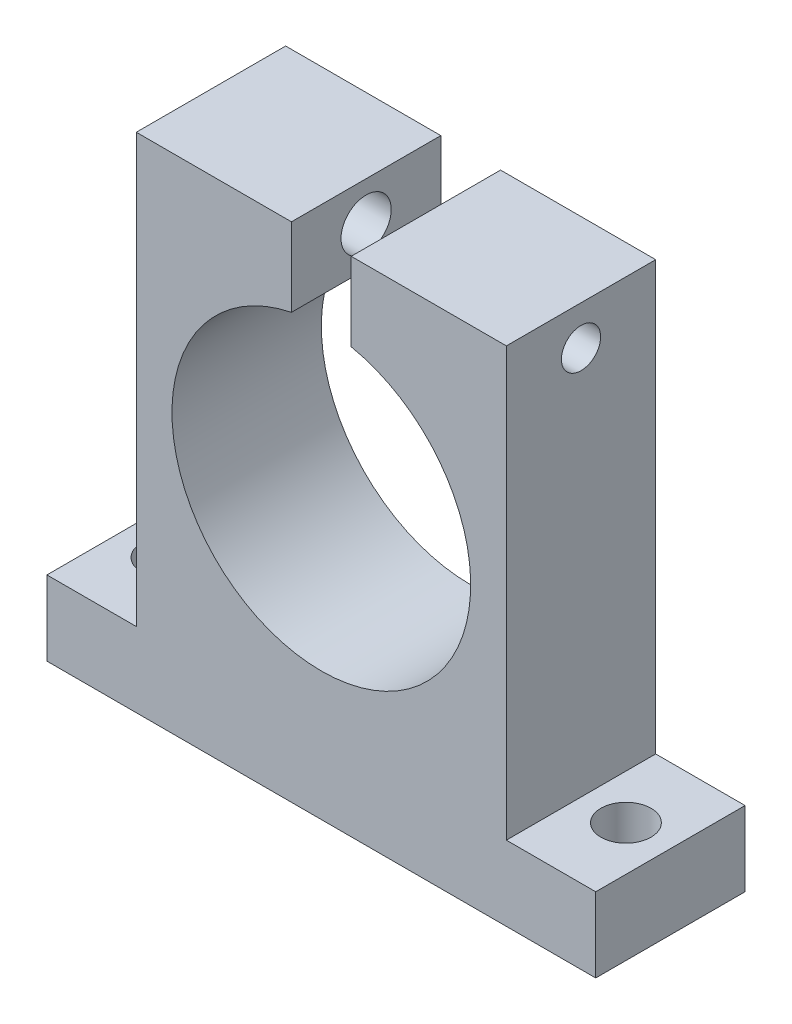
SolidWorks part; units mm, degrees
material "6061-T6 (SS)"
ref_plane "Front" through (0, 0, 0) normal (0, 0, 1) x (1, 0, 0)
ref_plane "Top" through (0, 0, 0) normal (0, 1, 0) x (1, 0, 0)
ref_plane "Right" through (0, 0, 0) normal (1, 0, 0) x (0, 0, -1)
sketch "Sketch7" plane through (0, 0, 0) normal (0, 0, 1) x (1, 0, 0)
  line L0 (-11.8, 14.3326) -> (-1.905, 14.3326)
  line L1 (-17.5, -12.9674) -> (-17.5, -17.7304)
  line L2 (-17.5, -17.7304) -> (17.5, -17.7304)
  line L3 (17.5, -17.7304) -> (17.5, -12.9674)
  line L4 (-1.905, 14.3326) -> (-1.905, 9.3326)
  line L5 (1.905, 14.3326) -> (1.905, 9.3326)
  line L6 (1.905, 14.3326) -> (11.8, 14.3326)
  line L7 (-11.8, 14.3326) -> (-11.8, -12.9674)
  line L8 (-11.8, -12.9674) -> (-17.5, -12.9674)
  line L9 (11.8, 14.3326) -> (11.8, -12.9674)
  line L10 (11.8, -12.9674) -> (17.5, -12.9674)
  line L11 (-1.905, 14.3326) -> (1.905, 14.3326) construction
  line L12 (-11.8, -12.9674) -> (11.8, -12.9674) construction
  arc A0 (-1.905, 9.3326) -> (1.905, 9.3326) centre (0, 0) ccw
  point P1 (-11.8, -12.9674)
  point P3 (9.525, 0)
  point P4 (0, 14.3326)
  point P5 (0, -17.7304)
  point P6 (0, -9.525)
  point P10 (-9.525, 0)
  point P12 (11.8, -12.9674)
  point P15 (-11.8, -12.9674)
  dimension "D1" = 5.7
  dimension "D3" = 27.3
  dimension "D6" = 5
  dimension "D7" = 4.763
  dimension "D2" = 35
  dimension "D5" = 32.063
extrude "Boss-Extrude3" add sketch "Sketch7" along normal blind 9.525
hole_wizard "Tap Drill for M3x0.5 Tap1" positions "Sketch11" profile "Sketch10" hole size "M3x0.5" standard "ANSI Metric" end condition up to next
sketch "Sketch11" plane through (11.8, 0, 0) normal (1, 0, 0) x (0, 0, -1)
  line L0 (-4.7625, 14.3326) -> (-4.7625, -12.9674) construction
  line L1 (-9.525, 14.3326) -> (0, 14.3326) construction
  line L2 (-9.525, -12.9674) -> (0, -12.9674) construction
  point P9 (-4.7625, 11.8326)
  dimension "D1" = 2.5
sketch "Sketch10" plane through (11.8, 11.8326, 4.7625) normal (0, 1, 0) x (0, 0, -1)
  line L0 (0, 0) -> (0, 9.895)
  line L1 (0, 9.895) -> (1.25, 9.895)
  line L2 (1.25, 9.895) -> (1.25, 0)
  line L5 (1.25, 0) -> (0, 0)
  line L11 (0, -6.35) -> (0, 107.95) construction
  dimension "Thru Hole Dia." = 2.5
  dimension "Thru Hole Depth" = 9.895
hole_wizard "M3 Clearance Hole1" positions "Sketch15" profile "Sketch14" hole size "M3" standard "ANSI Metric" end condition through all
sketch "Sketch15" plane through (0, -12.9674, 0) normal (0, 1, 0) x (1, 0, 0)
  line L0 (-11.8, 0) -> (-17.5, 0) construction
  line L1 (-17.5, -9.525) -> (-17.5, 0) construction
  point P0 (-14.65, -4.7496)
  dimension "D1" = 4.7496
  dimension "D2" = 2.85
sketch "Sketch14" plane through (-14.65, -12.9674, 4.7496) normal (1, 0, 0) x (0, 0, 1)
  line L0 (0, 0) -> (0, 4.763)
  line L1 (0, 4.763) -> (1.6, 4.763)
  line L2 (1.6, 4.763) -> (1.6, 0)
  line L5 (1.6, 0) -> (0, 0)
  line L11 (0, -6.35) -> (0, 107.95) construction
  dimension "Thru Hole Dia." = 3.2
  dimension "Thru Hole Depth" = 4.763
hole_wizard "M3 Clearance Hole2" positions "Sketch17" profile "Sketch16" hole size "M3" standard "ANSI Metric"
sketch "Sketch17" plane through (0, -12.9674, 0) normal (0, 1, 0) x (1, 0, 0)
  line L0 (17.5, 0) -> (11.8, 0) construction
  line L1 (17.5, -9.525) -> (17.5, 0) construction
  point P0 (14.65, -4.7496)
  dimension "D1" = 4.7496
  dimension "D2" = 2.85
sketch "Sketch16" plane through (14.65, -12.9674, 4.7496) normal (1, 0, 0) x (0, 0, 1)
  line L0 (0, 0) -> (0, 5.7214)
  line L1 (0, 5.7214) -> (1.6, 4.76)
  line L2 (1.6, 4.76) -> (1.6, 0)
  line L5 (1.6, 0) -> (0, 0)
  line L10 (0, 5.7214) -> (-1.6, 4.76) construction
  line L11 (0, -6.35) -> (0, 107.95) construction
  dimension "Hole Dia." = 3.2
  dimension "Hole Depth" = 4.76
  dimension "Drill Angle" = 118
hole_wizard "M3 Clearance Hole3" positions "Sketch19" profile "Sketch18" hole size "M3" standard "ANSI Metric" end condition up to next
sketch "Sketch19" plane through (-11.8, 0, 0) normal (-1, 0, 0) x (0, 0, 1)
  line L0 (9.525, 14.3326) -> (0, 14.3326) construction
  line L2 (4.7625, 14.3326) -> (4.7625, -12.9674) construction
  line L3 (9.525, -12.9674) -> (0, -12.9674) construction
  point P0 (4.7625, 11.8326)
  point P3 (4.7625, 14.3326)
  dimension "D1" = 2.5
sketch "Sketch18" plane through (-11.8, 11.8326, 4.7625) normal (0, 1, 0) x (0, 0, 1)
  line L0 (0, 0) -> (0, 9.895)
  line L1 (0, 9.895) -> (1.6, 9.895)
  line L2 (1.6, 9.895) -> (1.6, 0)
  line L5 (1.6, 0) -> (0, 0)
  line L11 (0, -6.35) -> (0, 107.95) construction
  dimension "Thru Hole Dia." = 3.2
  dimension "Thru Hole Depth" = 9.895
